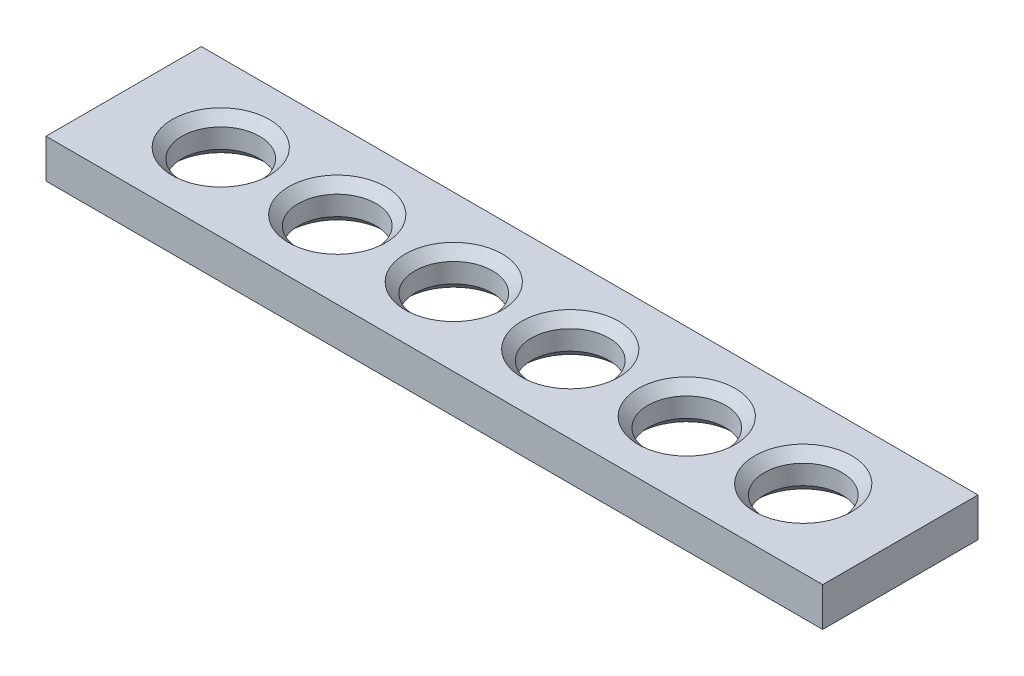
SolidWorks part; units mm, degrees
ref_plane "Alzado" through (0, 0, 0) normal (0, 0, 1) x (1, 0, 0)
ref_plane "Planta" through (0, 0, 0) normal (0, 1, 0) x (1, 0, 0)
ref_plane "Vista lateral" through (0, 0, 0) normal (1, 0, 0) x (0, 0, -1)
sketch "Croquis2" plane through (0, 0, 0) normal (1, 0, 0) x (0, 0, -1)
  line L1 (-12.7, -3.175) -> (12.7, -3.175)
  line L2 (-12.7, -3.175) -> (-12.7, 3.175)
  line L3 (-12.7, 3.175) -> (12.7, 3.175)
  line L4 (12.7, -3.175) -> (12.7, 3.175)
  line L5 (-12.7, -3.175) -> (12.7, 3.175) construction
  line L6 (-12.7, 3.175) -> (12.7, -3.175) construction
  point P0 (0, 0)
  dimension "D1" = 6.35
  dimension "D2" = 25.4
extrude "Saliente-Extruir1" add sketch "Croquis2" along normal blind 127
hole_wizard "Taladro1" positions "Croquis3" profile "Croquis5" legacy end condition through all
sketch "Croquis3" plane through (0, 3.175, 0) normal (0, 1, 0) x (1, 0, 0)
  line L0 (127, -12.7) -> (0, -12.7) construction
  point P0 (15.875, 0)
  dimension "D1" = 15.875
  dimension "D3" = 12.7
sketch "Croquis5" plane through (15.875, 3.175, 0) normal (1, 0, 0) x (0, 0, 1)
  line L0 (0, 0) -> (0, 6.35)
  line L1 (0, 6.35) -> (6.35, 6.35)
  line L2 (6.35, 6.35) -> (6.35, 0)
  line L3 (6.35, 0) -> (0, 0)
  line L4 (0, 110) -> (0, -10) construction
  dimension "Diámetro" = 12.7
  dimension "Profundidad" = 6.35
chamfer "Chaflán1" distance 1.5875 angle 45 2 edges at (15.875, 3.175, 6.35) (15.875, -3.175, 6.35)
pattern_linear "MatrizL1" count 6 spacing 19.05 along (1, 0, 0) of "Taladro1", "Chaflán1"
